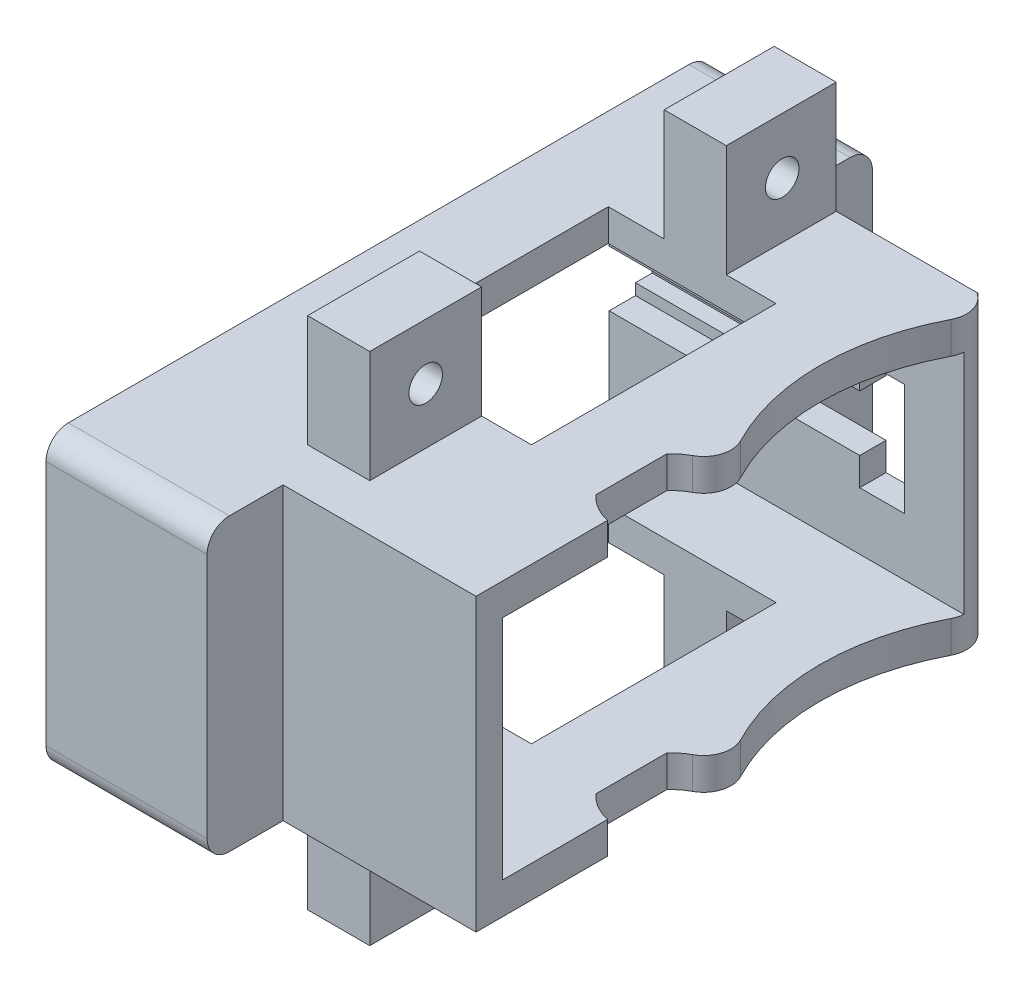
SolidWorks part; units mm, degrees
material "ABS"
ref_plane "Спереди" through (0, 0, 0) normal (0, 0, 1) x (1, 0, 0)
ref_plane "Сверху" through (0, 0, 0) normal (0, 1, 0) x (1, 0, 0)
ref_plane "Справа" through (0, 0, 0) normal (1, 0, 0) x (0, 0, -1)
sketch "Эскиз1" plane through (0, 0, 0) normal (0, 1, 0) x (1, 0, 0)
  line L4 (-47.15, 10.1488) -> (-17.7084, 10.1488)
  line L5 (-47.15, 10.1488) -> (-47.15, -30.7512)
  line L6 (-47.15, -30.7512) -> (-20.25, -30.7512)
  line L7 (-20.25, -30.7512) -> (-20.25, -13.7503)
  arc A4 (-17.9732, -9.3288) -> (-17.9732, 9.3288) centre (0, 0) cw
  arc A5 (-19.0472, -12.8153) -> (-17.9732, -9.3288) centre (-20.2808, -10.5266) ccw
  arc A6 (-17.9732, 9.3288) -> (-17.7084, 10.1488) centre (-20.2808, 10.5266) ccw
  arc A7 (-19.0472, -12.8153) -> (-20.25, -13.7503) centre (-16.8645, -16.8645) ccw
  dimension "D3" = 17.0009
  dimension "D4" = 2.6
  dimension "D5" = 4.6
  dimension "D9" = 2.6
  dimension "D11" = 3.4865
  dimension "D12" = 0.935
  dimension "D1" = 20.25
  dimension "D2" = 29.4416
  dimension "D6" = 40.9
  dimension "D7" = 26.9
  dimension "D8" = 0.82
  dimension "D13" = 18.6577
  dimension "D14" = 0.2647
  dimension "D15" = 1.074
extrude "Бобышка-Вытянуть1" add sketch "Эскиз1" along normal blind 3
pattern_linear "Линейный массив2" count 2 spacing 23 along (0, 1, 0) of bodies 103
sketch "Эскиз2" plane through (0, 26, 0) normal (0, 1, 0) x (1, 0, 0)
  line L0 (-17.7084, 10.1488) -> (-47.15, 10.1488)
  line L1 (-47.15, 10.1488) -> (-47.15, 19.4388)
  line L2 (-47.15, 19.4388) -> (-35.15, 19.4388)
  line L3 (-35.15, 19.4388) -> (-35.15, 12.6488)
  line L4 (-35.15, 12.6488) -> (-18.7788, 12.6488)
  line L5 (-20.25, -30.7512) -> (-47.15, -30.7512)
  line L6 (-47.15, -30.7512) -> (-47.15, -40.0412)
  line L7 (-47.15, -40.0412) -> (-35.15, -40.0412)
  line L8 (-35.15, -40.0412) -> (-35.15, -33.2512)
  line L9 (-35.15, -33.2512) -> (-17.75, -33.2512)
  line L10 (-17.75, -33.2512) -> (-17.75, -21.3785)
  line L11 (-20.25, -30.7512) -> (-20.25, -19.9787)
  line L12 (-35.15, -33.2512) -> (-35.15, -30.7512) construction
  line L13 (-20.25, -30.7512) -> (-17.75, -30.7512) construction
  line L15 (-20.25, -30.7512) -> (-20.25, -13.7503) construction
  circle A0 centre (0, 0) radius 20.25 construction
  circle A1 centre (-20.2808, -10.5266) radius 2.6 construction
  circle A2 centre (-16.8645, -16.8645) radius 4.6 construction
  circle A3 centre (-20.2808, 10.5266) radius 2.6 construction
  arc A4 (-19.0472, -12.8153) -> (-17.9732, -9.3288) centre (-20.2808, -10.5266) ccw construction
  arc A5 (-18.7788, 12.6488) -> (-17.7084, 10.1488) centre (-20.2808, 10.5266) cw
  arc A6 (-17.75, -21.3785) -> (-20.25, -19.9787) centre (-16.8645, -16.8645) cw
  line M11 (-17.7084, 10.1488) -> (-47.15, 10.1488)
  line M13 (-47.15, -30.7512) -> (-20.25, -30.7512)
  line M14 (-20.25, -30.7512) -> (-20.25, -13.7503)
  dimension "D4" = 40.5
  dimension "D1" = 9.29
  dimension "D2" = 12
  dimension "D3" = 2.5
extrude "Бобышка-Вытянуть2" add sketch "Эскиз2" against normal through all contours A5 L4 L3 L2 L1 M11 | L10 A6 L6 L7 L8 L9 M14 M13
sketch "Эскиз3" plane through (-47.15, 0, 0) normal (-1, 0, 0) x (0, 0, 1)
  line L0 (-19.4388, 13) -> (40.0412, 13) construction
  line L1 (-19.4388, 0) -> (-19.4388, 26) construction
  line L2 (40.0412, 0) -> (40.0412, 26) construction
  line L3 (10.3012, 26) -> (10.3012, 0) construction
  line L4 (40.0412, 26) -> (-19.4388, 26) construction
  line L5 (-19.4388, 0) -> (40.0412, 0) construction
  line L6 (-10.1488, 3) -> (-10.1488, 23) construction
  circle A0 centre (-13.9488, 8) radius 1.85
  circle A1 centre (-13.9488, 18) radius 1.85
  circle A2 centre (34.5512, 18) radius 1.85
  circle A3 centre (34.5512, 8) radius 1.85
  dimension "D1" = 3.7
  dimension "D2" = 5
  dimension "D3" = 3.8
extrude "Вырез-Вытянуть1" cut sketch "Эскиз3" against normal blind 10
sketch "Эскиз4" plane through (-47.15, 0, 0) normal (-1, 0, 0) x (0, 0, 1)
  line L0 (-10.1488, 3) -> (-10.1488, 23) construction
  line L1 (-10.1488, 15.5) -> (-12.6488, 15.5)
  line L2 (-10.1488, 15.5) -> (-10.1488, 10.5)
  line L3 (-10.1488, 10.5) -> (-12.6488, 10.5)
  line L4 (-12.6488, 10.5) -> (-12.6488, 11.5)
  line L5 (-12.6488, 11.5) -> (-14.1488, 11.5)
  line L6 (-14.1488, 11.5) -> (-14.1488, 14.5)
  line L7 (-14.1488, 14.5) -> (-12.6488, 14.5)
  line L8 (-12.6488, 14.5) -> (-12.6488, 15.5)
  line L9 (-10.1488, 10.5) -> (-10.1488, 3) construction
  line L10 (-10.1488, 23) -> (-10.1488, 15.5) construction
  dimension "D1" = 2.5
  dimension "D2" = 5
  dimension "D3" = 3
  dimension "D4" = 1.5
extrude "Вырез-Вытянуть2" cut sketch "Эскиз4" against normal blind 24
sketch "Эскиз5" plane through (0, 0, -12.6488) normal (0, 0, -1) x (-1, 0, 0)
  line L0 (23.15, 15.5) -> (23.15, 10.5) construction
  line L1 (23.15, 18) -> (27.15, 18)
  line L2 (23.15, 18) -> (23.15, 8)
  line L3 (23.15, 8) -> (27.15, 8)
  line L4 (27.15, 18) -> (27.15, 8)
  point P6 (23.15, 13)
  dimension "D1" = 4
  dimension "D2" = 10
extrude "Вырез-Вытянуть3" cut sketch "Эскиз5" against normal up to next
sketch "Эскиз6" plane through (-35.15, 0, 0) normal (1, 0, 0) x (0, 0, -1)
  line L0 (19.4388, 0) -> (19.4388, 26) construction
  line L1 (12.6488, 19) -> (14.6488, 19)
  line L2 (12.6488, 19) -> (12.6488, 7)
  line L3 (12.6488, 7) -> (14.6488, 7)
  line L4 (14.6488, 19) -> (14.6488, 7)
  line L5 (12.6488, 0) -> (12.6488, 10.5) construction
  point P4 (14.6488, 13)
  point P7 (19.4388, 13)
  dimension "D1" = 12
  dimension "D2" = 2
extrude "Бобышка-Вытянуть3" [suppressed] add sketch "Эскиз6" along normal up to surface (8 mm away)
fillet "Скругление1" [suppressed] radius 2
fillet "Скругление3" radius 2 4 edges at (-41.15, 26, 40.0412) (-41.15, 0, 40.0412) (-41.15, 26, -19.4388) (-41.15, 0, -19.4388)
sketch "Эскиз7" plane through (-47.15, 0, 0) normal (-1, 0, 0) x (0, 0, 1)
  line L0 (38.0412, 26) -> (-17.4388, 26) construction
  line L1 (-12.6488, 26) -> (-2.8188, 26)
  line L2 (-12.6488, 26) -> (-12.6488, 36)
  line L3 (-12.6488, 36) -> (-2.8188, 36)
  line L4 (-2.8188, 26) -> (-2.8188, 36)
  line L5 (-17.4388, 0) -> (38.0412, 0) construction
  line L6 (19.0512, 26) -> (29.0512, 26)
  line L7 (19.0512, 26) -> (19.0512, 36)
  line L8 (19.0512, 36) -> (29.0512, 36)
  line L9 (29.0512, 26) -> (29.0512, 36)
  line L10 (-12.6488, 0) -> (-2.8188, 0)
  line L11 (-12.6488, 0) -> (-12.6488, -10)
  line L12 (-12.6488, -10) -> (-2.8188, -10)
  line L13 (-2.8188, 0) -> (-2.8188, -10)
  line L14 (-19.4388, 2) -> (-19.4388, 24) construction
  line L15 (19.0512, 0) -> (29.0512, 0)
  line L16 (19.0512, 0) -> (19.0512, -10)
  line L17 (19.0512, -10) -> (29.0512, -10)
  line L18 (29.0512, 0) -> (29.0512, -10)
  dimension "D1" = 9.83
  dimension "D2" = 10
  dimension "D3" = 10
  dimension "D4" = 6.79
  dimension "D5" = 21.87
extrude "Бобышка-Вытянуть4" add sketch "Эскиз7" against normal blind 5.55 from offset 10 offset against normal yes
sketch "Эскиз8" plane through (-37.15, 0, 0) normal (-1, 0, 0) x (0, 0, 1)
  line L0 (29.0512, -10) -> (19.0512, 0) construction
  line L1 (29.0512, 26) -> (19.0512, 36) construction
  line L3 (-17.4388, 0) -> (38.0412, 0) construction
  line L4 (-2.8188, -10) -> (-12.8188, -10) construction
  line L5 (-2.8188, -10) -> (-2.8188, 0) construction
  line L6 (-2.8188, 0) -> (-12.8188, 0) construction
  line L7 (-12.8188, -10) -> (-12.8188, 0) construction
  line L8 (38.0412, 26) -> (-17.4388, 26) construction
  line L9 (-2.8188, 36) -> (-12.8188, 36) construction
  line L10 (-2.8188, 36) -> (-2.8188, 26) construction
  line L11 (-2.8188, 26) -> (-12.8188, 26) construction
  line L12 (-12.8188, 36) -> (-12.8188, 26) construction
  line L13 (-2.8188, -10) -> (-12.8188, 0) construction
  line L14 (-2.8188, 26) -> (-12.8188, 36) construction
  circle A0 centre (-7.8188, -5) radius 1.5
  circle A1 centre (-7.8188, 31) radius 1.5
  circle A2 centre (24.0512, 31) radius 1.5
  circle A3 centre (24.0512, -5) radius 1.5
  dimension "D2" = 3
  dimension "D1" = 10
extrude "Вырез-Вытянуть4" cut sketch "Эскиз8" against normal up to next
sketch "Эскиз10" plane through (0, 0, 0) normal (0, -1, 0) x (1, 0, 0)
  line L0 (-31.6, 19.0512) -> (-37.15, 19.0512) construction
  line L1 (-42.15, 19.0512) -> (-27.15, 19.0512)
  line L2 (-42.15, 19.0512) -> (-42.15, -2.8188)
  line L3 (-42.15, -2.8188) -> (-27.15, -2.8188)
  line L4 (-27.15, 19.0512) -> (-27.15, -2.8188)
  line L5 (-31.6, -2.8188) -> (-37.15, -2.8188) construction
  line L6 (-47.15, -17.4388) -> (-47.15, 38.0412) construction
  dimension "D1" = 5
  dimension "D2" = 15
extrude "Вырез-Вытянуть5" cut sketch "Эскиз10" against normal through all
sketch "Эскиз11" plane through (0, 26, 0) normal (0, 1, 0) x (1, 0, 0)
  line L0 (-17.75, -21.3785) -> (-17.75, -33.2512)
  line L2 (-20.25, -19.9787) -> (-20.25, -13.7503)
  line L3 (-17.9, -21.5003) -> (-17.9, -33.2512)
  line L4 (-18.7788, 12.6488) -> (-18.9288, 12.6488)
  line L5 (-35.15, -33.2512) -> (-17.75, -33.2512) construction
  line L6 (-20.4, -13.6923) -> (-20.4, -20.0367)
  line L7 (-18.9288, 12.5698) -> (-18.9288, 12.6488)
  line L8 (-31.6, 12.6488) -> (-18.7788, 12.6488) construction
  arc A0 (-17.9732, 9.3288) -> (-18.7788, 12.6488) centre (-20.2808, 10.5266) ccw
  arc A1 (-20.25, -19.9787) -> (-17.75, -21.3785) centre (-16.8645, -16.8645) ccw construction
  arc A2 (-17.9732, 9.3288) -> (-17.9732, -9.3288) centre (0, 0) ccw
  arc A3 (-19.0472, -12.8153) -> (-17.9732, -9.3288) centre (-20.2808, -10.5266) ccw
  arc A4 (-20.25, -19.9787) -> (-17.75, -21.3785) centre (-16.8645, -16.8645) ccw
  arc A5 (-17.9732, 9.3288) -> (-17.9732, -9.3288) centre (0, 0) ccw construction
  arc A6 (-17.9732, 9.3288) -> (-18.7788, 12.6488) centre (-20.2808, 10.5266) ccw construction
  arc A7 (-19.0472, -12.8153) -> (-17.9732, -9.3288) centre (-20.2808, -10.5266) ccw construction
  arc A8 (-19.0472, -12.8153) -> (-20.25, -13.7503) centre (-16.8645, -16.8645) ccw
  arc A9 (-18.1063, 9.398) -> (-18.9288, 12.5698) centre (-20.2808, 10.5266) ccw
  arc A10 (-18.1063, 9.398) -> (-18.1063, -9.398) centre (0, 0) ccw
  arc A11 (-19.1183, -12.6833) -> (-18.1063, -9.398) centre (-20.2808, -10.5266) ccw
  arc A12 (-19.1183, -12.6833) -> (-20.4, -13.6923) centre (-16.8645, -16.8645) ccw
  arc A13 (-20.4, -20.0367) -> (-17.9, -21.5003) centre (-16.8645, -16.8645) ccw
  dimension "D2" = 20.25
  dimension "D1" = 2.6
  dimension "D3" = 2.6
  dimension "D4" = 4.6
  dimension "D5" = 4.6
  dimension "D6" = 4.9
  dimension "D7" = 40.8
  dimension "D8" = 9.5
  dimension "D11" = 0.15
  dimension "D9" = 0.15
  dimension "D10" = 0.15
extrude "Вырез-Вытянуть6" cut sketch "Эскиз11" against normal through all and the other way through all
sketch "Эскиз12" plane through (-47.15, 0, 0) normal (-1, 0, 0) x (0, 0, 1)
  line L0 (-19.4388, 2) -> (-19.4388, 24) construction
  line L1 (-17.4388, 26) -> (38.0412, 26)
  line L2 (-19.4388, 24) -> (-19.4388, 2)
  line L3 (-17.4388, 0) -> (38.0412, 0)
  line L4 (40.0412, 24) -> (40.0412, 2)
  line L5 (40.0412, 2) -> (40.0412, 24) construction
  line L6 (38.0412, 26) -> (-17.4388, 26) construction
  line L7 (-17.4388, 0) -> (38.0412, 0) construction
  line L8 (-10.1488, 23) -> (-10.1488, 15.5)
  line L9 (-10.1488, 23) -> (30.7512, 23)
  line L10 (-10.1488, 15.5) -> (-12.6488, 15.5)
  line L11 (-10.1488, 3) -> (30.7512, 3)
  line L12 (30.7512, 23) -> (30.7512, 3)
  line L13 (-12.6488, 15.5) -> (-12.6488, 14.5)
  line L14 (-12.6488, 8) -> (-12.6488, 18) construction
  line L15 (-12.6488, 14.5) -> (-14.1488, 14.5)
  line L16 (-14.1488, 14.5) -> (-14.1488, 11.5)
  line L17 (-14.1488, 11.5) -> (-12.6488, 11.5)
  line L18 (-12.6488, 11.5) -> (-12.6488, 10.5)
  line L19 (-12.6488, 10.5) -> (-10.1488, 10.5)
  line L20 (-10.1488, 10.5) -> (-10.1488, 3)
  circle A0 centre (34.5512, 18) radius 1.85
  circle A1 centre (-13.9488, 18) radius 1.85
  circle A2 centre (-13.9488, 8) radius 1.85
  circle A3 centre (34.5512, 8) radius 1.85
  arc A4 (38.0412, 26) -> (40.0412, 24) centre (38.0412, 24) cw
  arc A5 (38.0412, 0) -> (40.0412, 2) centre (38.0412, 2) ccw
  arc A6 (-19.4388, 2) -> (-17.4388, 0) centre (-17.4388, 2) ccw
  arc A7 (-17.4388, 26) -> (-19.4388, 24) centre (-17.4388, 24) ccw
  dimension "D1" = 2
extrude "Бобышка-Вытянуть5" add sketch "Эскиз12" along normal blind 2.4
sketch "Эскиз13" plane through (-20.25, 0, 0) normal (-1, 0, 0) x (0, 0, 1)
  line L1 (20.1963, 23) -> (30.7512, 23)
  line L2 (20.1963, 23) -> (20.1963, 3)
  line L3 (20.1963, 3) -> (30.7512, 3)
  line L4 (30.7512, 23) -> (30.7512, 3)
extrude "Вырез-Вытянуть7" cut sketch "Эскиз13" against normal through all
sketch "Эскиз14" plane through (-49.55, 0, 0) normal (-1, 0, 0) x (0, 0, 1)
  line L0 (30.7512, 23) -> (-10.1488, 23) construction
  line L1 (-10.2988, 23.15) -> (30.9012, 23.15)
  line L2 (-10.2988, 23.15) -> (-10.2988, 2.85)
  line L3 (-10.2988, 2.85) -> (30.9012, 2.85)
  line L4 (30.9012, 23.15) -> (30.9012, 2.85)
  line L5 (-10.1488, 3) -> (30.7512, 3) construction
  line L6 (30.7512, 3) -> (30.7512, 23) construction
  line L7 (-10.1488, 10.5) -> (-10.1488, 3) construction
  dimension "D1" = 0.15
  dimension "D2" = 0.15
  dimension "D3" = 0.15
  dimension "D4" = 0.15
extrude "Вырез-Вытянуть8" cut sketch "Эскиз14" against normal through all
